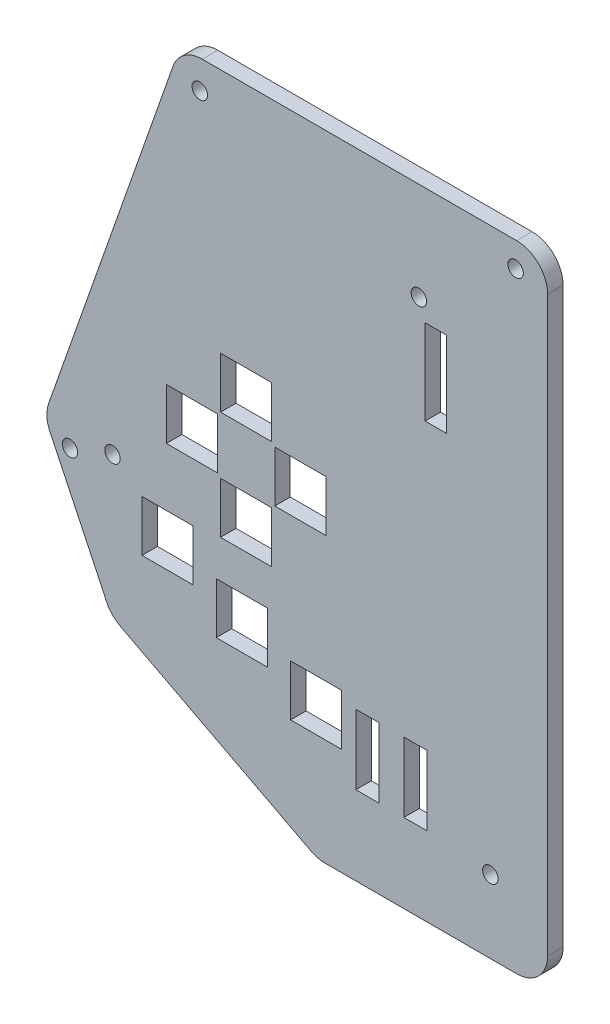
SolidWorks part; units mm, degrees
ref_plane "Front Plane" through (0, 0, 0) normal (0, 0, 1) x (1, 0, 0)
ref_plane "Top Plane" through (0, 0, 0) normal (0, 1, 0) x (1, 0, 0)
ref_plane "Right Plane" through (0, 0, 0) normal (1, 0, 0) x (0, 0, -1)
sketch "Sketch1" plane through (0, 0, 0) normal (0, 0, 1) x (1, 0, 0)
  line L6 (-20.066, -57.15) -> (46.99, -57.15) construction
  line L7 (-12.446, -73.152) -> (46.99, -73.152) construction
  line L8 (-3.3141, 6.35) -> (48.26, 6.35)
  line L9 (53.34, 1.27) -> (53.34, -92.71)
  line L10 (48.26, -97.79) -> (16.847, -97.79)
  line L16 (-8.1072, 2.9529) -> (-28.5162, -55.1739)
  line L18 (-20.066, -57.15) -> (-29.21, -57.15) construction
  line L26 (0, 0) -> (46.99, 0) construction
  line L27 (46.99, 0) -> (46.99, -88.9) construction
  line L28 (46.99, -88.9) -> (17.78, -88.9) construction
  line L29 (17.78, -88.9) -> (-12.446, -73.152) construction
  line L30 (-12.446, -73.152) -> (-20.066, -57.15) construction
  line L31 (-20.066, -57.15) -> (0, 0) construction
  line L32 (46.99, -57.15) -> (46.99, -88.9) construction
  line L33 (17.78, -88.9) -> (15.603, -97.79) construction
  line L34 (-12.446, -73.152) -> (-17.9301, -78.4424) construction
  line L35 (14.4997, -97.2152) -> (-16.7505, -80.9336)
  line L36 (-28.3096, -59.0409) -> (-18.9898, -78.6124)
  arc A0 (53.34, -92.71) -> (48.26, -97.79) centre (48.26, -92.71) cw
  arc A1 (14.4997, -97.2152) -> (16.847, -97.79) centre (16.847, -92.71) ccw
  arc A2 (-16.7505, -80.9336) -> (-18.9898, -78.6124) centre (-14.4033, -76.4284) cw
  arc A3 (-28.5162, -55.1739) -> (-28.3096, -59.0409) centre (-23.723, -56.8568) ccw
  arc A4 (-8.1072, 2.9529) -> (-3.3141, 6.35) centre (-3.3141, 1.27) cw
  arc A5 (48.26, 6.35) -> (53.34, 1.27) centre (48.26, 1.27) cw
  point P13 (53.34, -97.79)
  point P32 (53.34, 6.35)
  dimension "D8" = 5.08
  dimension "D1" = 88.9
  dimension "D2" = 29.21
  dimension "D3" = 59.436
  dimension "D4" = 67.056
  dimension "D5" = 104.14
  dimension "D6" = 82.55
  dimension "D7" = 46.99
  dimension "D13" = 103.76
  dimension "D17" = 108.51
sketch "Sketch3" plane through (0, 0, 0) normal (0, 0, 1) x (1, 0, 0)
  line L6 (-20.066, -57.15) -> (46.99, -57.15) construction
  line L7 (-12.446, -73.152) -> (46.99, -73.152) construction
  line L8 (0, 0) -> (46.99, 0) construction
  line L9 (46.99, 0) -> (46.99, -88.9) construction
  line L10 (46.99, -88.9) -> (17.78, -88.9) construction
  line L11 (17.78, -88.9) -> (-12.446, -73.152) construction
  line L12 (-12.446, -73.152) -> (-20.066, -57.15) construction
  line L13 (-20.066, -57.15) -> (0, 0) construction
  line L14 (3.8784, -55.88) -> (3.8784, -38.1) construction
  circle A0 centre (3.8784, -38.1) radius 5.08
  circle A1 centre (-5.0116, -46.99) radius 5.08
  circle A2 centre (3.8784, -55.88) radius 5.08
  circle A3 centre (12.7684, -46.99) radius 5.08
  circle A4 centre (-9.144, -65.024) radius 5.08
  circle A5 centre (3.048, -70.612) radius 5.08
  circle A6 centre (15.24, -76.2) radius 5.08
  dimension "D7" = 10.16
  dimension "D1" = 43.1116
  dimension "D2" = 8.89
  dimension "D3" = 8.89
  dimension "D4" = 46.99
  dimension "D5" = 8.89
  dimension "D6" = 8.89
  dimension "D8" = 12.192
  dimension "D9" = 5.588
  dimension "D10" = 5.588
  dimension "D11" = 12.192
  dimension "D12" = 43.942
  dimension "D13" = 70.612
sketch "Sketch10" plane through (0, 0, 0) normal (0, 0, 1) x (1, 0, 0)
  line L1 (53.34, 1.27) -> (53.34, -92.71)
  line L6 (48.26, -97.79) -> (16.847, -97.79)
  line L16 (-8.1072, 2.9529) -> (-28.5162, -55.1739)
  line L19 (53.34, 1.27) -> (53.34, -92.71) construction
  line L21 (-8.1072, 2.9529) -> (-28.5162, -55.1739) construction
  line L24 (14.4997, -97.2152) -> (-16.7505, -80.9336)
  line L25 (-18.9898, -78.6124) -> (-28.3096, -59.0409)
  line L26 (-3.3141, 6.35) -> (48.26, 6.35)
  arc A0 (-18.9898, -78.6124) -> (-16.7505, -80.9336) centre (-14.4033, -76.4284) ccw
  arc A1 (16.847, -97.79) -> (14.4997, -97.2152) centre (16.847, -92.71) cw
  arc A2 (-28.5162, -55.1739) -> (-28.3096, -59.0409) centre (-23.723, -56.8568) ccw
  arc A3 (53.34, -92.71) -> (48.26, -97.79) centre (48.26, -92.71) cw
  arc A4 (-8.1072, 2.9529) -> (-3.3141, 6.35) centre (-3.3141, 1.27) cw
  arc A5 (48.26, 6.35) -> (53.34, 1.27) centre (48.26, 1.27) cw
  point P13 (15.603, -97.79)
  point P17 (-29.21, -57.15)
  point P20 (53.34, -97.79)
  dimension "D1" = 5.08
extrude "Boss-Extrude1" add sketch "Sketch10" along normal blind 2.54
sketch "Sketch11" plane through (0, 0, 2.54) normal (0, 0, 1) x (1, 0, 0)
  line L0 (46.99, -88.9) -> (17.78, -88.9) construction
  line L5 (33.561, -73.406) -> (29.751, -73.406)
  line L6 (33.561, -73.406) -> (33.561, -84.836)
  line L11 (33.561, -84.836) -> (29.751, -84.836)
  line L12 (29.751, -73.406) -> (29.751, -84.836)
  line L18 (46.99, 0) -> (46.99, -88.9) construction
  line L23 (25.687, -73.406) -> (21.877, -73.406)
  line L24 (25.687, -73.406) -> (25.687, -84.836)
  line L29 (25.687, -84.836) -> (21.877, -84.836)
  line L30 (21.877, -73.406) -> (21.877, -84.836)
  line L42 (8.0694, -51.689) -> (-0.3126, -51.689)
  line L43 (8.0694, -51.689) -> (8.0694, -60.071)
  line L44 (8.0694, -60.071) -> (-0.3126, -60.071)
  line L45 (-0.3126, -51.689) -> (-0.3126, -60.071)
  line L46 (-0.8206, -42.799) -> (-9.2026, -42.799)
  line L47 (-0.8206, -42.799) -> (-0.8206, -51.181)
  line L48 (-0.8206, -51.181) -> (-9.2026, -51.181)
  line L49 (-9.2026, -42.799) -> (-9.2026, -51.181)
  line L52 (8.0694, -42.291) -> (-0.3126, -42.291)
  line L53 (-0.3126, -33.909) -> (-0.3126, -42.291)
  line L54 (16.9594, -42.799) -> (8.5774, -42.799)
  line L55 (16.9594, -42.799) -> (16.9594, -51.181)
  line L56 (16.9594, -51.181) -> (8.5774, -51.181)
  line L57 (8.5774, -42.799) -> (8.5774, -51.181)
  line L58 (-0.3126, -33.909) -> (8.0694, -33.909)
  line L59 (8.0694, -33.909) -> (8.0694, -42.291)
  line L60 (3.8784, -51.689) -> (3.8784, -60.071) construction
  line L61 (-0.3126, -55.88) -> (8.0694, -55.88) construction
  line L62 (-5.0116, -51.181) -> (-5.0116, -42.799) construction
  line L63 (-9.2026, -46.99) -> (-0.8206, -46.99) construction
  line L64 (12.7684, -42.799) -> (12.7684, -51.181) construction
  line L65 (8.5774, -46.99) -> (16.9594, -46.99) construction
  line L66 (3.8784, -33.909) -> (3.8784, -42.291) construction
  line L67 (-0.3126, -38.1) -> (8.0694, -38.1) construction
  line L68 (-4.826, -60.706) -> (-4.826, -69.088)
  line L69 (-13.208, -65.024) -> (-5.08, -65.024) construction
  line L70 (-9.144, -60.96) -> (-9.144, -69.088) construction
  line L71 (-4.826, -69.088) -> (-13.208, -69.088)
  line L72 (-13.208, -60.706) -> (-13.208, -69.088)
  line L73 (-4.826, -60.706) -> (-13.208, -60.706)
  line L74 (7.366, -66.294) -> (7.366, -74.676)
  line L75 (-1.016, -70.612) -> (7.112, -70.612) construction
  line L76 (3.048, -66.548) -> (3.048, -74.676) construction
  line L77 (7.366, -74.676) -> (-1.016, -74.676)
  line L78 (-1.016, -66.294) -> (-1.016, -74.676)
  line L79 (7.366, -66.294) -> (-1.016, -66.294)
  line L80 (19.558, -71.882) -> (19.558, -80.264)
  line L81 (11.176, -76.2) -> (19.304, -76.2) construction
  line L82 (15.24, -72.136) -> (15.24, -80.264) construction
  line L83 (19.558, -80.264) -> (11.176, -80.264)
  line L84 (11.176, -71.882) -> (11.176, -80.264)
  line L85 (19.558, -71.882) -> (11.176, -71.882)
  dimension "D1" = 4.064
  dimension "D3" = 13.429
  dimension "D4" = 11.43
  dimension "D5" = 3.81
  dimension "D6" = 4.064
  dimension "D7" = 11.43
  dimension "D8" = 4.064
  dimension "D13" = 3.81
  dimension "D21" = 8.382
  dimension "D22" = 8.382
extrude "Cut-Extrude1" cut sketch "Sketch11" against normal through all both and the other way through all
sketch "Sketch12" plane through (0, 0, 0) normal (0, 0, -1) x (-1, 0, 0)
  line L0 (20.066, -57.15) -> (-46.99, -57.15) construction
  line L1 (-37.465, -31.4407) -> (-43.942, -85.852) construction
  line L2 (-46.99, 0) -> (-46.99, -88.9) construction
  line L5 (18.034, -57.15) -> (20.066, -57.15) construction
  line L10 (-46.99, -88.9) -> (-17.78, -88.9) construction
  circle A2 centre (18.034, -57.15) radius 1.27
  circle A3 centre (-43.942, -85.852) radius 1.27
  dimension "D1" = 2.54
  dimension "D6" = 2.032
  dimension "D3" = 54.7954
  dimension "D11" = 3.048
  dimension "D12" = 3.048
extrude "Cut-Extrude2" cut sketch "Sketch12" against normal through all both and the other way through all
sketch "Sketch13" plane through (0, 0, 0) normal (0, 0, -1) x (-1, 0, 0)
  line L0 (28.3096, -59.0409) -> (18.9898, -78.6124) construction
  line L1 (8.1072, 2.9529) -> (28.5162, -55.1739) construction
  line L2 (3.3141, 6.35) -> (-48.26, 6.35) construction
  line L4 (-53.34, 1.27) -> (-53.34, -92.71) construction
  circle A1 centre (25.0123, -59.762) radius 1.27
  circle A4 centre (-48.0822, 2.286) radius 1.27
  circle A5 centre (3.7187, 1.651) radius 1.27
  dimension "D1" = 2.54
  dimension "D2" = 4.826
  dimension "D4" = 4.064
  dimension "D3" = 2.667
  dimension "D5" = 5.2578
  dimension "D6" = 4.699
  dimension "D7" = 4.572
extrude "Cut-Extrude3" cut sketch "Sketch13" against normal through all both and the other way through all
sketch "Sketch14" plane through (0, 0, 0) normal (0, 0, -1) x (-1, 0, 0)
  line L0 (-36.7885, -26.7831) -> (-33.2325, -26.7831)
  line L1 (-36.7885, -12.8131) -> (-36.7885, -26.7831)
  line L2 (-33.2325, -12.8131) -> (-36.7885, -12.8131)
  line L3 (-33.2325, -12.8131) -> (-33.2325, -26.7831)
  line L4 (-53.34, 1.27) -> (-53.34, -92.71) construction
  line L5 (3.3141, 6.35) -> (-48.26, 6.35) construction
  dimension "D1" = 16.5515
  dimension "D2" = 13.97
  dimension "D3" = 19.1631
extrude "Cut-Extrude4" cut sketch "Sketch14" against normal through all both and the other way through all
sketch "Sketch16" plane through (0, 0, 0) normal (0, 0, -1) x (-1, 0, 0)
  line L0 (3.3141, 6.35) -> (-48.26, 6.35) construction
  line L1 (-53.34, 1.27) -> (-53.34, -92.71) construction
  circle A0 centre (-32.219, -9.6761) radius 1.27
  dimension "D1" = 16.0261
  dimension "D2" = 2.54
  dimension "D3" = 21.121
extrude "Cut-Extrude5" cut sketch "Sketch16" against normal through all both and the other way through all
